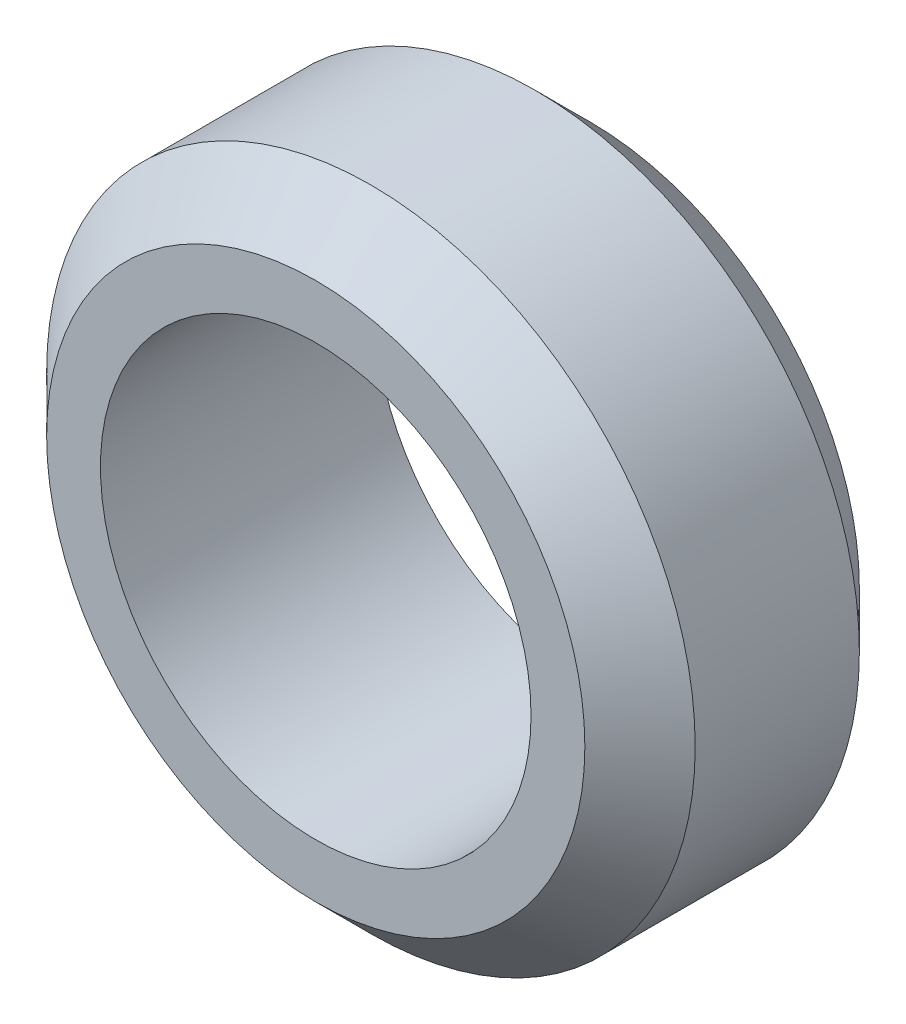
SolidWorks part; units mm, degrees
ref_plane "Front Plane" through (0, 0, 0) normal (0, 0, 1) x (1, 0, 0)
ref_plane "Top Plane" through (0, 0, 0) normal (0, 1, 0) x (1, 0, 0)
ref_plane "Right Plane" through (0, 0, 0) normal (1, 0, 0) x (0, 0, -1)
sketch "Sketch1" plane through (0, 0, 0) normal (0, 0, 1) x (1, 0, 0)
  circle A0 centre (0, 0) radius 12.05
  circle A1 centre (0, 0) radius 8
  dimension "D1" = 24.1
  dimension "D2" = 16
extrude "Boss-Extrude1" add sketch "Sketch1" along normal mid plane 10.2
chamfer "Chamfer1" distance 2.05 angle 45 2 edges at (12.05, 0, -5.1) (12.05, 0, 5.1)
